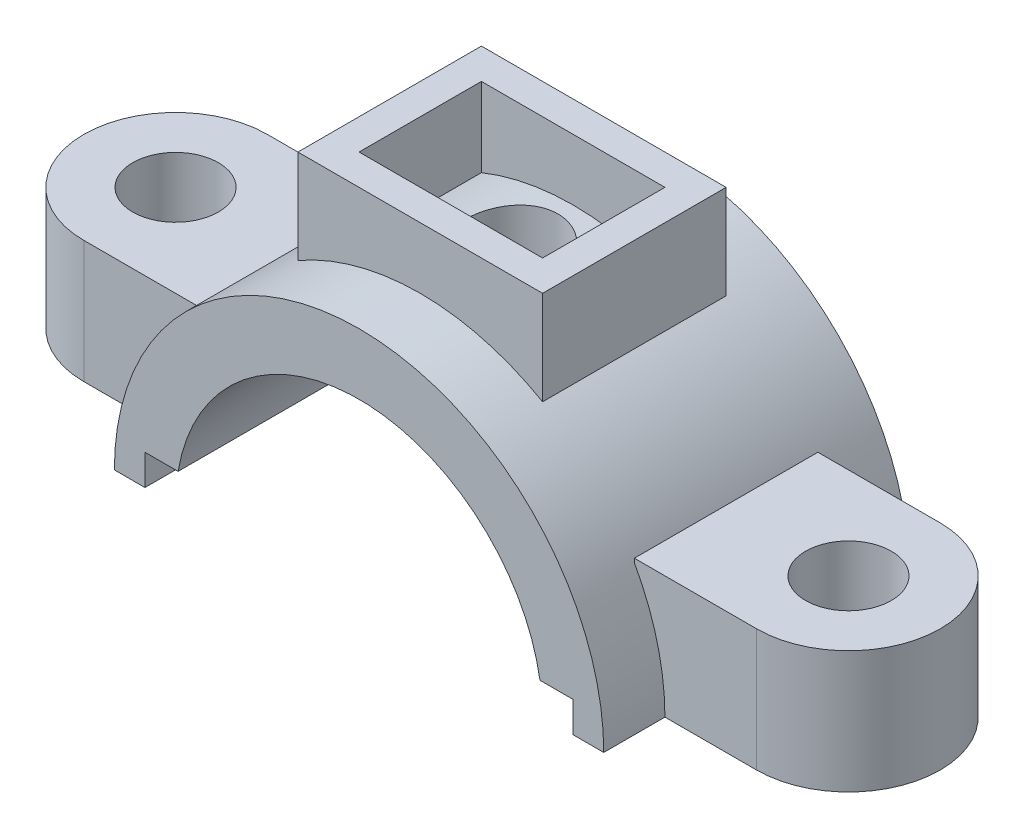
SolidWorks part; units mm, degrees
ref_plane "Front Plane" through (0, 0, 0) normal (0, 0, 1) x (1, 0, 0)
ref_plane "Top Plane" through (0, 0, 0) normal (0, 1, 0) x (1, 0, 0)
ref_plane "Right Plane" through (0, 0, 0) normal (1, 0, 0) x (0, 0, -1)
sketch "Sketch2" plane through (0, 0, 0) normal (0, 1, 0) x (1, 0, 0)
  line L0 (0, -55) -> (0, 55) construction
  line L1 (-55, 15) -> (-35, 15)
  line L2 (-35, 15) -> (-35, -15)
  line L3 (-35, -15) -> (-55, -15)
  line L4 (35, -15) -> (55, -15)
  line L5 (35, 15) -> (35, -15)
  line L6 (55, 15) -> (35, 15)
  circle A0 centre (-55, 0) radius 7
  arc A1 (-55, 15) -> (-55, -15) centre (-55, 0) ccw
  arc A2 (55, 15) -> (55, -15) centre (55, 0) cw
  circle A3 centre (55, 0) radius 7
  dimension "D1" = 55
extrude "Boss-Extrude1" add sketch "Sketch2" along normal blind 20
sketch "Sketch3" plane through (0, 0, 0) normal (0, 0, 1) x (1, 0, 0)
  line L0 (35, 0) -> (55, 0) construction
  line L1 (-40, 0) -> (-35, 0)
  line L2 (-35, 0) -> (-35, 5)
  line L3 (-35, 20) -> (-35, 0) construction
  line L4 (-35, 5) -> (-29.5804, 5)
  line L5 (0, -11) -> (0, 11) construction
  line L6 (35, 5) -> (29.5804, 5)
  line L7 (35, 0) -> (35, 5)
  line L8 (40, 0) -> (35, 0)
  arc A0 (40, 0) -> (-40, 0) centre (0, 0) ccw
  arc A1 (29.5804, 5) -> (-29.5804, 5) centre (0, 0) ccw
  arc A2 (-29.5804, 5) -> (29.5804, 5) centre (0, 0) cw
extrude "Boss-Extrude4" add sketch "Sketch3" along normal blind 25 and the other way blind 25 contours A1 L6 L7 L8 A0 L1 L2 L4
ref_plane "Plane2" through (0, 50, 0) normal (0, 1, 0) x (1, 0, 0)
sketch "Sketch5" plane through (0, 50, 0) normal (0, 1, 0) x (1, 0, 0)
  line L1 (-20, -15) -> (20, -15)
  line L2 (-20, -15) -> (-20, 15)
  line L3 (-20, 15) -> (20, 15)
  line L4 (20, -15) -> (20, 15)
  line L5 (-15, -10) -> (15, -10)
  line L6 (-15, -10) -> (-15, 10)
  line L7 (-15, 10) -> (15, 10)
  line L8 (15, -10) -> (15, 10)
  line L9 (-15, -10) -> (15, 10) construction
  line L10 (-15, 10) -> (15, -10) construction
  point P0 (0, 0)
  point P6 (0, 0)
extrude "Boss-Extrude5" add sketch "Sketch5" against normal up to surface (15.359 mm away)
sketch "Sketch6" plane through (0, 50, 0) normal (0, 1, 0) x (1, 0, 0)
  circle A0 centre (0, 0) radius 7.5
extrude "Cut-Extrude1" cut sketch "Sketch6" against normal through all
